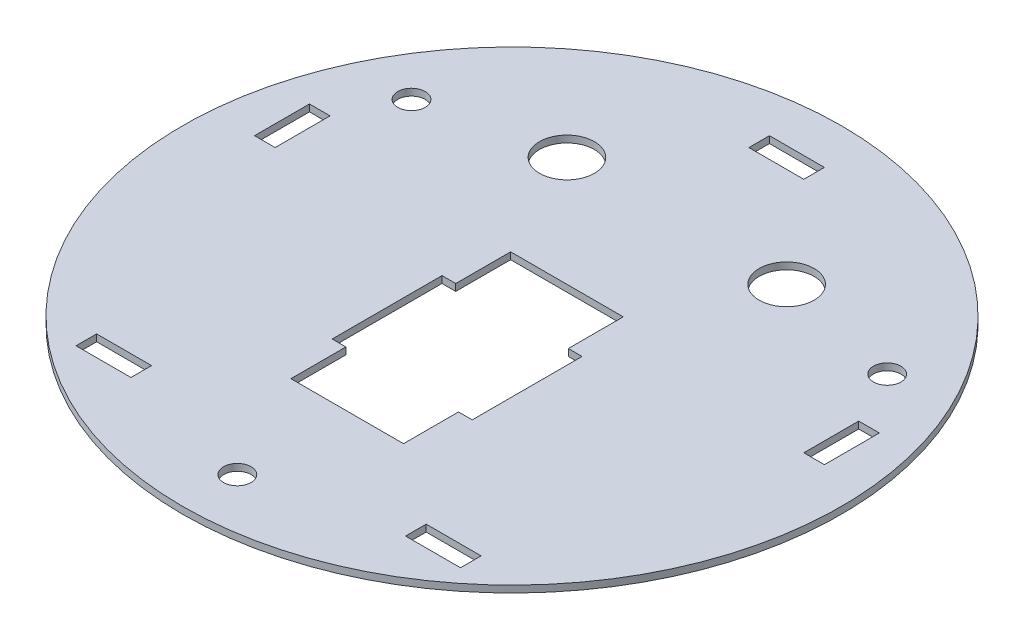
SolidWorks part; units mm, degrees
ref_plane "Front Plane" through (0, 0, 0) normal (0, 0, 1) x (1, 0, 0)
ref_plane "Top Plane" through (0, 0, 0) normal (0, 1, 0) x (1, 0, 0)
ref_plane "Right Plane" through (0, 0, 0) normal (1, 0, 0) x (0, 0, -1)
sketch "Sketch1" plane through (0, 0, 0) normal (0, 1, 0) x (1, 0, 0)
  line L0 (0, 152.4) -> (304.8, 152.4) construction
  line L1 (0, 0) -> (304.8, 0) construction
  line L2 (0, 0) -> (0, 304.8) construction
  line L3 (0, 304.8) -> (304.8, 304.8) construction
  line L4 (304.8, 0) -> (304.8, 304.8) construction
  line L5 (152.4, 304.8) -> (152.4, 0) construction
  circle A0 centre (152.4, 152.4) radius 152.4
  dimension "D1" = 304.8
  dimension "D2" = 304.8
extrude "Boss-Extrude1" add sketch "Sketch1" along normal blind 3.175
sketch "Sketch2" plane through (0, 3.175, 0) normal (0, 1, 0) x (1, 0, 0)
  line L0 (152.4, 152.4) -> (0, 152.4) construction
  line L1 (152.4, 152.4) -> (304.8, 152.4) construction
  line L2 (152.4, 152.4) -> (284.3823, 228.6) construction
  line L3 (152.4, 0) -> (284.3823, 228.6) construction
  line L4 (284.3823, 228.6) -> (20.4177, 228.6) construction
  line L5 (20.4177, 228.6) -> (152.4, 0) construction
  line L6 (152.4, 152.4) -> (20.4177, 228.6) construction
  line L7 (152.4, 152.4) -> (152.4, 127) construction
  line L8 (76.2, 44.45) -> (228.6, 44.45) construction
  line L9 (152.4, 152.4) -> (152.4, 304.8) construction
  line L10 (241.3, 39.6875) -> (215.9, 39.6875)
  line L11 (241.3, 39.6875) -> (241.3, 49.2125)
  line L12 (241.3, 49.2125) -> (215.9, 49.2125)
  line L13 (215.9, 39.6875) -> (215.9, 49.2125)
  line L14 (241.3, 39.6875) -> (215.9, 49.2125) construction
  line L15 (241.3, 49.2125) -> (215.9, 39.6875) construction
  line L16 (63.5, 39.6875) -> (88.9, 39.6875)
  line L17 (63.5, 39.6875) -> (63.5, 49.2125)
  line L18 (63.5, 49.2125) -> (88.9, 49.2125)
  line L19 (88.9, 39.6875) -> (88.9, 49.2125)
  line L20 (63.5, 39.6875) -> (88.9, 49.2125) construction
  line L21 (101.6, 241.3) -> (203.2, 241.3) construction
  line L22 (178.435, 127) -> (126.365, 127) construction
  line L23 (184.785, 101.6123) -> (178.435, 101.6123)
  line L24 (184.785, 101.6123) -> (184.785, 152.4123)
  line L25 (184.785, 152.4123) -> (178.435, 152.4123)
  line L26 (126.365, 177.8) -> (126.365, 152.4123)
  line L27 (126.365, 101.6123) -> (120.015, 101.6123)
  line L28 (178.435, 177.8) -> (178.435, 152.4123)
  line L29 (126.365, 152.4123) -> (120.015, 152.4123)
  line L30 (120.015, 101.6123) -> (120.015, 152.4123)
  line L31 (152.4, 0) -> (152.4, 127) construction
  line L32 (126.365, 76.2) -> (126.365, 101.6123)
  line L33 (126.365, 177.8) -> (178.435, 177.8)
  line L34 (178.435, 101.6123) -> (178.435, 76.2)
  line L35 (126.365, 76.2) -> (178.435, 76.2)
  line L36 (63.5, 49.2125) -> (88.9, 39.6875) construction
  line L37 (126.365, 177.8) -> (178.435, 76.2) construction
  line L38 (126.365, 76.2) -> (178.435, 177.8) construction
  line L40 (139.7, 284.1625) -> (165.1, 284.1625)
  line L41 (139.7, 284.1625) -> (139.7, 274.6375)
  line L42 (139.7, 274.6375) -> (165.1, 274.6375)
  line L43 (165.1, 284.1625) -> (165.1, 274.6375)
  line L44 (139.7, 284.1625) -> (165.1, 274.6375) construction
  line L45 (139.7, 274.6375) -> (165.1, 284.1625) construction
  line L46 (274.6375, 190.5) -> (284.1625, 190.5)
  line L47 (274.6375, 190.5) -> (274.6375, 165.1)
  line L48 (274.6375, 165.1) -> (284.1625, 165.1)
  line L49 (284.1625, 190.5) -> (284.1625, 165.1)
  line L50 (274.6375, 190.5) -> (284.1625, 165.1) construction
  line L51 (274.6375, 165.1) -> (284.1625, 190.5) construction
  line L52 (20.6375, 190.5) -> (30.1625, 190.5)
  line L53 (20.6375, 190.5) -> (20.6375, 165.1)
  line L54 (20.6375, 165.1) -> (30.1625, 165.1)
  line L55 (30.1625, 190.5) -> (30.1625, 165.1)
  line L56 (20.6375, 190.5) -> (30.1625, 165.1) construction
  line L57 (20.6375, 165.1) -> (30.1625, 190.5) construction
  circle A0 centre (42.4148, 215.9) radius 6.35
  circle A1 centre (152.4, 25.4) radius 6.35
  circle A2 centre (152.4, 152.4) radius 152.4 construction
  circle A3 centre (262.3852, 215.9) radius 6.35
  circle A4 centre (152.4, 152.4) radius 76.2 construction
  circle A5 centre (101.6, 228.6) radius 12.7
  circle A6 centre (203.2, 228.6) radius 12.7
  point P22 (152.4, 44.45)
  point P29 (279.4, 177.8)
  point P31 (152.4, 279.4)
  point P57 (25.4, 177.8)
  dimension "D5" = 12.7
  dimension "D3" = 12.7
  dimension "D2" = 12.7
  dimension "D4" = 127
  dimension "D12" = 127
  dimension "D13" = 127
  dimension "D29" = 25.4
  dimension "D30" = 50.8
  dimension "D6" = 6.35
  dimension "D7" = 6.35
  dimension "D8" = 50.8
  dimension "D9" = 52.07
  dimension "D10" = 127
  dimension "D11" = 101.6
  dimension "D14" = 152.4
  dimension "D15" = 107.95
  dimension "D16" = 25.4
  dimension "D17" = 25.4
  dimension "D18" = 9.525
  dimension "D19" = 127
  dimension "D20" = 9.525
  dimension "D21" = 9.525
  dimension "D22" = 25.4
  dimension "D23" = 25.4
  dimension "D24" = 25.4
  dimension "D25" = 127
  dimension "D26" = 25.4
  dimension "D27" = 127
  dimension "D28" = 9.525
  dimension "D31" = 50.8
extrude "Cut-Extrude1" cut sketch "Sketch2" against normal blind 3.175
